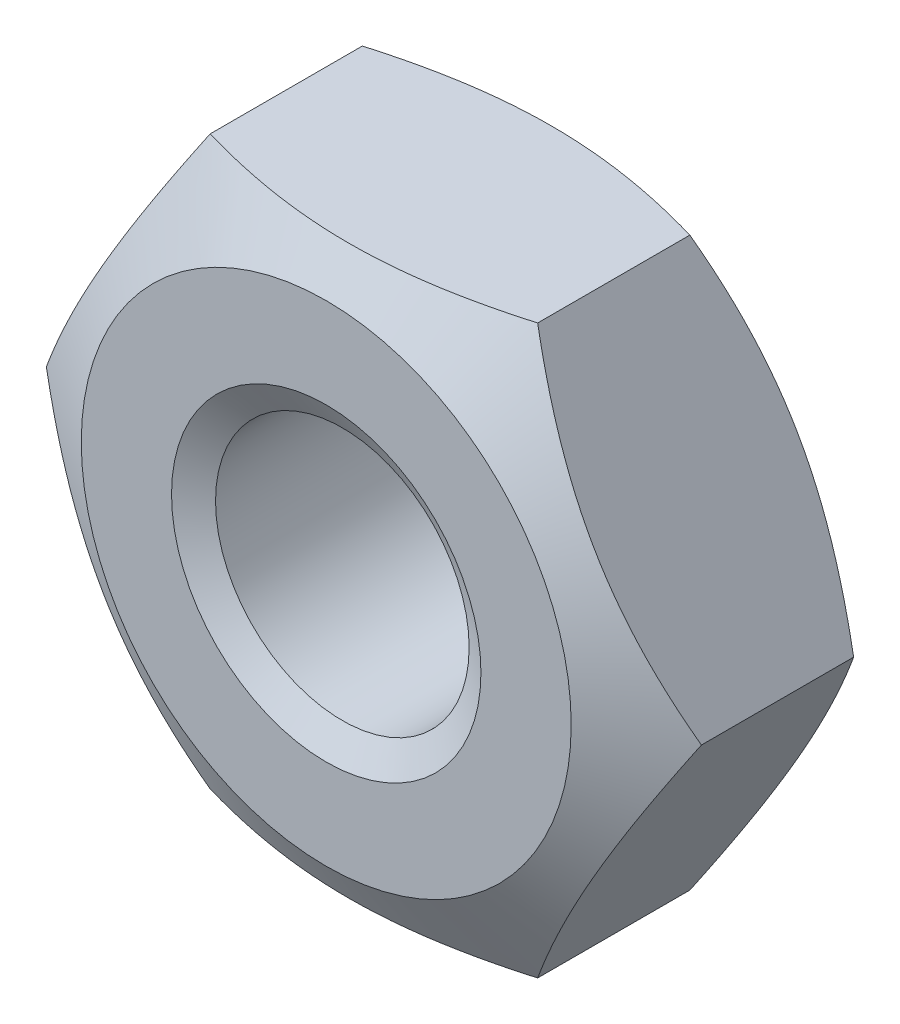
SolidWorks part; units mm, degrees
ref_plane "Front" through (0, 0, 0) normal (0, 0, 1) x (1, 0, 0)
ref_plane "Top" through (0, 0, 0) normal (0, 1, 0) x (1, 0, 0)
ref_plane "Right" through (0, 0, 0) normal (1, 0, 0) x (0, 0, -1)
sketch "Sketch1" plane through (0, 0, 0) normal (0, 0, 1) x (1, 0, 0)
  line L1 (3.1754, 0) -> (1.5877, 2.75)
  line L2 (1.5877, 2.75) -> (-1.5877, 2.75)
  line L3 (-1.5877, 2.75) -> (-3.1754, 0)
  line L4 (-3.1754, 0) -> (-1.5877, -2.75)
  line L5 (-1.5877, -2.75) -> (1.5877, -2.75)
  line L6 (1.5877, -2.75) -> (3.1754, 0)
  circle A0 centre (0, 0) radius 2.75 construction
  circle A1 centre (0, 0) radius 1.2295
  dimension "D" = 2.459
  dimension "s" = 5.5
extrude "BaseNut" add sketch "Sketch1" against normal blind 2.4
cosmetic thread "ThreadCosmetic1" [suppressed] parameters "D"=3
sketch "Sketch2" plane through (0, 0, 0) normal (0, 1, 0) x (1, 0, 0)
  line L0 (-3.1754, 2.4) -> (-2.375, 2.4)
  line L2 (-2.375, 2.4) -> (-3.1754, 1.9379)
  line L3 (-3.1754, 1.9379) -> (-3.1754, 2.4)
  line L4 (0, 3.3759) -> (0, -9.8171) construction
  line L6 (-9.7712, 1.2) -> (9.8853, 1.2) construction
  line L7 (-3.1754, 0.4621) -> (-3.1754, 0)
  line L8 (-2.375, 0) -> (-3.1754, 0.4621)
  line L9 (-3.1754, 0) -> (-2.375, 0)
  dimension "dw" = 4.75
  dimension "D1" = 30
  dimension "D2" = 1.2
revolve "Double-Chamfer" cut sketch "Sketch2" angle 360 about L4
chamfer "EndChamfer" distance 0.2705 angle 30 2 edges at (1.2295, 0, -2.4) (1.2295, 0, 0)
sketch "Sketch3" plane through (0, 0, 0) normal (0, 1, 0) x (1, 0, 0)
  line L0 (-1.4638, 2.1295) -> (-1.2295, 1.9942)
  line L1 (-1.2295, 1.9942) -> (-0.959, 1.9942)
  line L2 (-0.959, 1.9942) -> (-0.959, 2.2647)
  line L3 (-0.959, 2.2647) -> (-1.2295, 2.2647)
  line L4 (-1.2295, 2.2647) -> (-1.4638, 2.1295)
  line L5 (0, 7.4383) -> (0, 16.8806) construction
  dimension "D1" = 0.2705
  dimension "D2" = 2.459
revolve "Cut-Revolve10" [suppressed] cut sketch "Sketch3" angle 360 about L5
pattern_linear "LPattern10" [suppressed] count 7 spacing 0.3246 along (0, 0, -1)
equation "\"dw@Sketch2\" = \"s@Sketch1\"-0.75"
equation "\"D2@Sketch2\" = \"m@BaseNut\" / 2"
equation "\"D2@Sketch3\" = \"D@Sketch1\""
equation "\"D1@Sketch3\" =  (\"D@ThreadCosmetic1\"   - \"D@Sketch1\")  / 2"
equation "\"D3@LPattern10\" = \"D1@Sketch3\" * 1.2"
equation "\"D1@LPattern10\" = \"m@BaseNut\"/\"D3@LPattern10\""
